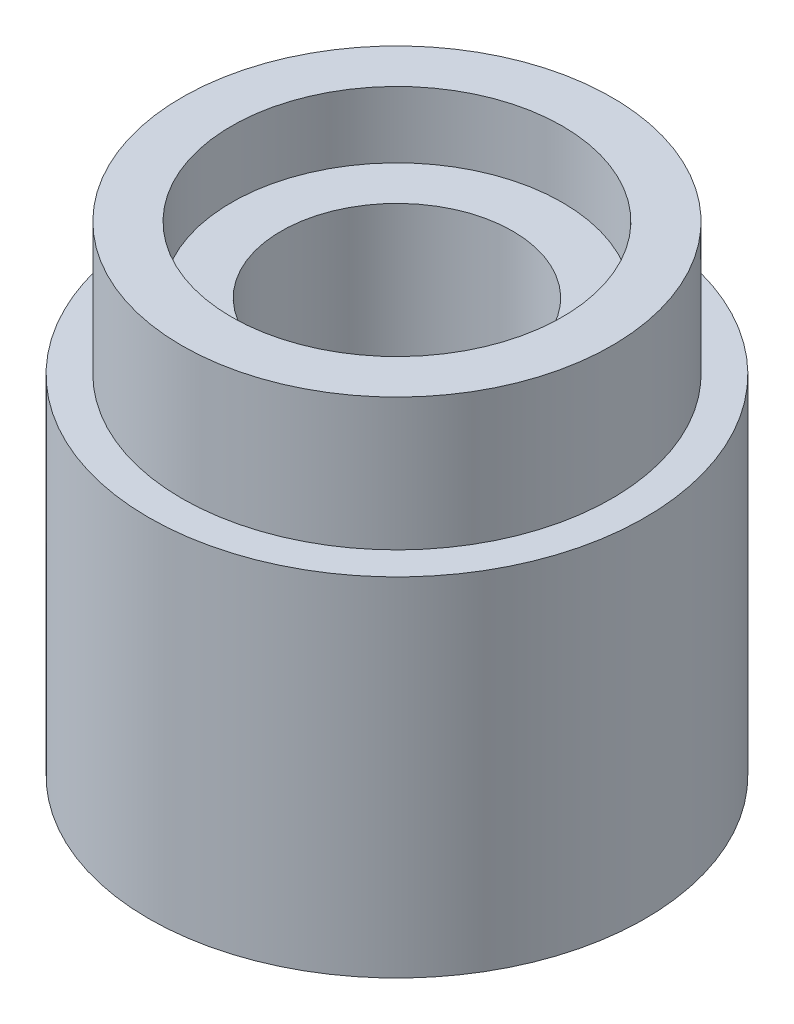
SolidWorks part; units mm, degrees
ref_plane "Front Plane" through (0, 0, 0) normal (0, 0, 1) x (1, 0, 0)
ref_plane "Top Plane" through (0, 0, 0) normal (0, 1, 0) x (1, 0, 0)
ref_plane "Right Plane" through (0, 0, 0) normal (1, 0, 0) x (0, 0, -1)
sketch "Sketch1" plane through (0, 0, 0) normal (0, 1, 0) x (1, 0, 0)
  circle A0 centre (0, 0) radius 3.75
extrude "Boss-Extrude1" add sketch "Sketch1" along normal blind 7.25
sketch "Sketch2" plane through (0, 7.25, 0) normal (0, 1, 0) x (1, 0, 0)
  circle A0 centre (0, 0) radius 2.5
  circle A1 centre (0, 0) radius 3.75
sketch "Sketch3" plane through (0, 7.25, 0) normal (0, 1, 0) x (1, 0, 0)
  circle A0 centre (0, 0) radius 3.25
  circle A1 centre (0, 0) radius 3.75
extrude "Cut-Extrude1" cut sketch "Sketch3" against normal blind 2
sketch "Sketch4" plane through (0, 7.25, 0) normal (0, 1, 0) x (1, 0, 0)
  circle A0 centre (0, 0) radius 1.75
extrude "Cut-Extrude2" cut sketch "Sketch4" against normal blind 6.75
sketch "Sketch5" plane through (0, 7.25, 0) normal (0, 1, 0) x (1, 0, 0)
  circle A0 centre (0, 0) radius 2.5
extrude "Cut-Extrude3" cut sketch "Sketch5" against normal blind 1
